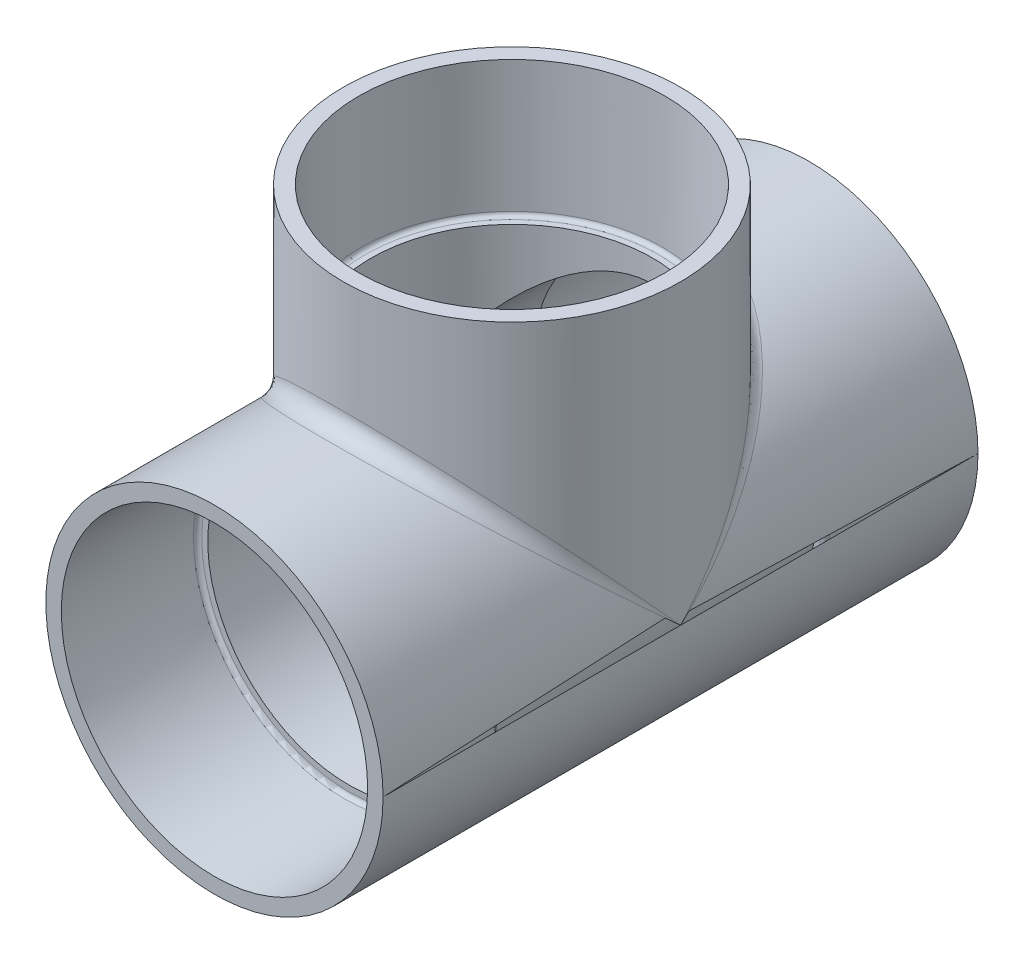
SolidWorks part; units mm, degrees
ref_plane "Front" through (0, 0, 0) normal (0, 0, 1) x (1, 0, 0)
ref_plane "Top" through (0, 0, 0) normal (0, 1, 0) x (1, 0, 0)
ref_plane "Right" through (0, 0, 0) normal (1, 0, 0) x (0, 0, -1)
sketch "Sketch1" plane through (0, 0, 0) normal (1, 0, 0) x (0, 0, -1)
  line L0 (-168.7051, 0) -> (102.8272, 0) construction
  line L1 (-112.7125, 63.8969) -> (112.7125, 63.8969)
  line L6 (112.7125, 63.8969) -> (112.7125, 58.0367)
  line L8 (-112.7125, 58.0367) -> (-112.7125, 63.8969)
  line L11 (-112.7125, 58.0367) -> (-61.9125, 57.15)
  line L12 (-61.9125, 57.15) -> (-61.9125, 53.34)
  line L13 (-61.9125, 53.34) -> (61.9125, 53.34)
  line L14 (61.9125, 53.34) -> (61.9125, 57.15)
  line L15 (61.9125, 57.15) -> (112.7125, 58.0367)
  line L16 (0, 53.34) -> (0, 0) construction
  dimension "D5" = 1
  dimension "D6" = 106.68
  dimension "D1" = 127.7937
  dimension "D2" = 225.425
  dimension "D3" = 114.3
  dimension "D4" = 61.9125
revolve "Revolve1" add sketch "Sketch1" angle 360 about L0
ref_plane "Plane1" through (0, 112.7125, 0) normal (0, 1, 0) x (1, 0, 0)
sketch "Sketch2" plane through (0, 112.7125, 0) normal (0, 1, 0) x (1, 0, 0)
  line L0 (63.8969, -112.7125) -> (63.8969, 112.7125) construction
  circle A0 centre (0, 0) radius 63.8969
extrude "Boss-Extrude1" add sketch "Sketch2" against normal up to surface (48.8156 mm away)
sketch "Sketch3" plane through (0, 0, 0) normal (1, 0, 0) x (0, 0, -1)
  line L0 (-58.0367, 112.7125) -> (-57.15, 61.9125)
  line L1 (70.2866, 112.7125) -> (-70.2866, 112.7125) construction
  line L2 (-57.15, 61.9125) -> (0, 61.9125)
  line L3 (0, 61.9125) -> (0, 112.7125)
  line L4 (0, 112.7125) -> (-58.0367, 112.7125)
  line L5 (-63.8969, 112.7125) -> (-63.8969, 63.8969) construction
  line L6 (0, 0) -> (0, 41.3488) construction
  dimension "D1" = 1
  dimension "D2" = 61.9125
  dimension "D3" = 114.3
revolve "Cut-Revolve1" cut sketch "Sketch3" angle 360 about L6
sketch "Sketch4" plane through (0, 61.9125, 0) normal (0, 1, 0) x (1, 0, 0)
  circle A0 centre (0, 0) radius 53.34
  dimension "D1" = 106.68
extrude "Cut-Extrude1" cut sketch "Sketch4" against normal up to next
fillet "Fillet1" radius 1.5875 3 edges at (57.15, 0, -61.9125) (0, 61.9125, -57.15) (57.15, 0, 61.9125)
fillet "Fillet2" radius 6.35 2 edges at (0, 63.8969, 63.8969) (0, 63.8969, -63.8969)
